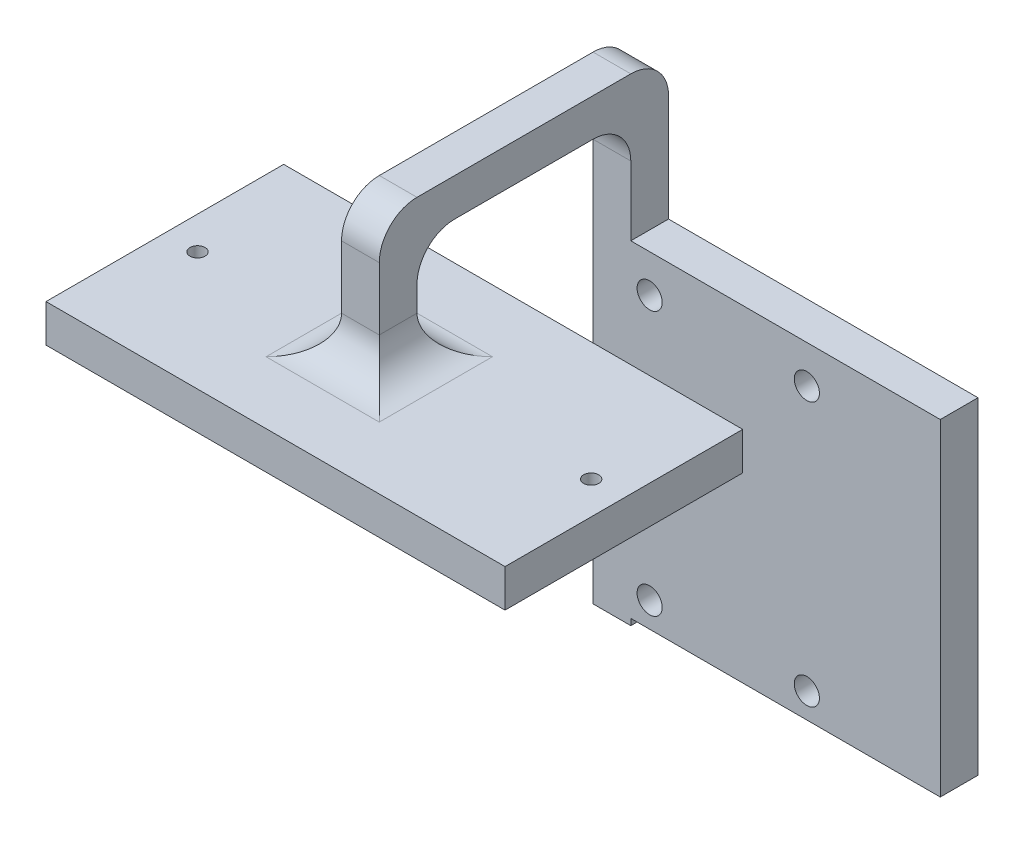
SolidWorks part; units mm, degrees
ref_plane "Ön Düzlem" through (0, 0, 0) normal (0, 0, 1) x (1, 0, 0)
ref_plane "Üst Düzlem" through (0, 0, 0) normal (0, 1, 0) x (1, 0, 0)
ref_plane "Sağ Düzlem" through (0, 0, 0) normal (1, 0, 0) x (0, 0, -1)
sketch "Çizim1" plane through (0, 0, 0) normal (0, 1, 0) x (1, 0, 0)
  line L13 (-14.05, 0) -> (-19.1293, 0) construction
  line L14 (0, 6.45) -> (0, 11.0365) construction
  line L22 (21.5293, 0) -> (16.45, 0) construction
  line L23 (0, -11.0365) -> (0, -6.45) construction
  line L24 (-19.1293, 11.0365) -> (21.5293, 11.0365)
  line L25 (-19.1293, 11.0365) -> (-19.1293, -11.0365)
  line L26 (-19.1293, -11.0365) -> (21.5293, -11.0365)
  line L27 (1.9, -6.45) -> (1.9, -3.2953)
  line L28 (1.9, -3.2953) -> (16.6263, -1.9922)
  line L29 (16.6263, 1.9922) -> (1.9, 3.2953)
  line L30 (1.9, 3.2953) -> (1.9, 6.45)
  line L31 (-1.9, 6.45) -> (-1.9, 2.8797)
  line L32 (-2.2091, 2.65) -> (-14.1591, 1.997)
  line L33 (-14.1591, -1.997) -> (-2.2091, -2.65)
  line L34 (-1.9, -2.8797) -> (-1.9, -6.45)
  line L35 (21.5293, 11.0365) -> (21.5293, -11.0365)
  arc A19 (-1.9, -6.45) -> (1.9, -6.45) centre (0, -6.45) ccw
  arc A20 (16.6263, -1.9922) -> (16.6263, 1.9922) centre (16.45, 0) ccw
  arc A21 (1.9, 6.45) -> (-1.9, 6.45) centre (0, 6.45) ccw
  arc A22 (-1.9, 2.8797) -> (-2.2091, 2.65) centre (0, 0) ccw
  arc A23 (-14.1591, 1.997) -> (-14.1591, -1.997) centre (-14.05, 0) ccw
  arc A24 (-2.2091, -2.65) -> (-1.9, -2.8797) centre (0, 0) ccw
extrude "Yükseklik-Ekstrüzyon3" add sketch "Çizim1" along normal blind 1.5
sketch "Çizim10" plane through (0, 1.5, 0) normal (0, 1, 0) x (1, 0, 0)
  line L4 (21.5293, -11.0365) -> (21.5293, 11.0365)
  line L5 (21.5293, 11.0365) -> (-19.1293, 11.0365)
  line L6 (-19.1293, 11.0365) -> (-19.1293, -11.0365)
  line L7 (-19.1293, -11.0365) -> (21.5293, -11.0365)
  line L8 (21.5293, -11.0365) -> (21.5293, 11.0365)
  line L9 (21.5293, 11.0365) -> (-19.1293, 11.0365)
  line L10 (-19.1293, 11.0365) -> (-19.1293, -11.0365)
  line L11 (-19.1293, -11.0365) -> (21.5293, -11.0365)
  dimension "D1" = 0
extrude "Yükseklik-Ekstrüzyon5" add sketch "Çizim10" along normal blind 1.5
sketch "Çizim11" plane through (0, 0, 0) normal (1, 0, 0) x (0, 0, -1)
  line L2 (18.5, 10.9809) -> (1.5, 10.9809)
  line L3 (18.5, 10.9809) -> (18.5, -24.0191)
  line L4 (1.5, 1.7777) -> (1.5, 10.9809)
  line L5 (1.5, 13.9809) -> (21.5, 13.9809)
  line L6 (21.5, 13.9809) -> (21.5, -24.0191)
  line L7 (-1.5, 1.7777) -> (-1.5, 10.9809)
  line L8 (18.5, -24.0191) -> (21.5, -24.0191)
  line L9 (1.5, 1.7777) -> (-1.5, 1.7777)
  line L10 (0, 1.7777) -> (0, 10.9809) construction
  line L11 (18.5, 10.9809) -> (18.5, 13.9809) construction
  line L12 (18.5, 12.4809) -> (-13.0492, 12.4809) construction
  line L13 (18.5, 12.4809) -> (21.5, 12.4809) construction
  line L14 (20, 12.4809) -> (20, -24.0191) construction
  line L15 (1.5, 13.9809) -> (-1.5, 13.9809)
  line L16 (-1.5, 13.9809) -> (-1.5, 10.9809)
  line L18 (0, 12.4809) -> (0, 15.9654) construction
  dimension "D1" = 20
  dimension "D2" = 3
  dimension "D3" = 3
  dimension "D4" = 3
  dimension "D5" = 36.5
extrude "Yükseklik-Ekstrüzyon6" add sketch "Çizim11" along normal mid plane 3
sketch "Çizim12" plane through (0, 0, 0) normal (0, 1, 0) x (1, 0, 0)
  line L0 (-14.05, 0) -> (-17.05, 0) construction
  line L1 (19.45, 0) -> (16.45, 0) construction
  line L2 (0, -6.45) -> (0, -9.45) construction
  line L3 (0, 9.45) -> (0, 6.45) construction
  line L4 (0, -9.45) -> (-17.05, -9.45)
  line L5 (-17.05, -9.45) -> (-17.05, 9.45)
  line L6 (-17.05, 9.45) -> (19.45, 9.45)
  line L7 (19.45, 9.45) -> (19.45, -9.45)
  line L8 (19.45, -9.45) -> (0, -9.45)
  line L10 (-19.1293, -11.0365) -> (21.5293, -11.0365)
  line L11 (-19.1293, -11.0365) -> (-19.1293, 11.0365)
  line L12 (-19.1293, 11.0365) -> (21.5293, 11.0365)
  line L13 (21.5293, -11.0365) -> (21.5293, 11.0365)
  dimension "D1" = 3
  dimension "D2" = 3
extrude "Kes-Ekstrüzyon1" cut sketch "Çizim12" along normal blind 5 and the other way blind 3
fillet "Radyus1" radius 3 8 edges at (0, 3, -1.5) (-1.5, 3, 0) (1.5, 3, 0) (0, 3, 1.5) (0, 13.9809, 1.5) (0, 10.9809, -1.5) (0, 13.9809, -21.5) (0, 10.9809, -18.5)
ref_plane "Düzlem1" through (0, 0, -20) normal (0, 0, -1) x (-1, 0, 0)
sketch "Çizim13" plane through (0, 0, -20) normal (0, 0, -1) x (-1, 0, 0)
  line L0 (-26.1083, 2.483) -> (-26.1083, -23.517)
  line L3 (0.8917, 2.483) -> (0.8917, -2.4979)
  line L8 (0.8917, 2.483) -> (-26.1083, 2.483)
  line L16 (0.8917, -23.517) -> (-26.1083, -23.517)
  line L22 (0.8917, -2.4979) -> (0.8917, -23.517)
  point P0 (-12.6083, -23.517)
  dimension "D2" = 27
  dimension "D1" = 26
extrude "Yükseklik-Ekstrüzyon7" add sketch "Çizim13" along normal up to surface and the other way up to surface up to face at (0, -6.5191, -21.5) other way up to face at (0, -8.0191, -18.5)
sketch "Çizim18" plane through (0, 1.5, 0) normal (0, -1, 0) x (1, 0, 0)
  line L0 (-16.05, 0) -> (-14.45, 0) construction
  line L1 (18.45, 0) -> (16.85, 0) construction
  arc A0 (-14.1591, 1.997) -> (-14.1591, -1.997) centre (-14.05, 0) ccw construction
  circle A1 centre (-14.45, 0) radius 0.6
  arc A2 (16.6263, -1.9922) -> (16.6263, 1.9922) centre (16.45, 0) ccw construction
  circle A3 centre (16.85, 0) radius 0.6
extrude "Kes-Ekstrüzyon3" cut sketch "Çizim18" against normal blind 3 and the other way blind 7
sketch "Sketch1" plane through (0, 0, -21.5) normal (0, 0, -1) x (-1, 0, 0)
  line L0 (-1.5, -23.517) -> (-26.1083, -23.517) construction
  line L1 (1.5, -24.0191) -> (1.5, 10.9809) construction
  line L2 (-26.1083, 2.483) -> (-1.5, 2.483) construction
  circle A0 centre (-2.999, -0.517) radius 1
  circle A1 centre (-2.999, -21.517) radius 1
  circle A2 centre (-15.499, -21.517) radius 1
  circle A3 centre (-15.499, -0.517) radius 1
  point P10 (0, 0)
  point P13 (0, 0)
  dimension "D1" = 2
  dimension "D2" = 2
  dimension "D3" = 2
  dimension "D4" = 2
  dimension "D7" = 2
  dimension "D5" = 21
  dimension "D6" = 21
  dimension "D8" = 3
  dimension "D9" = 3
  dimension "D10" = 2
  dimension "D11" = 12.5
  dimension "D12" = 12.5
  dimension "D13" = 4.499
extrude "Cut-Extrude1" cut sketch "Sketch1" against normal up to surface (3 mm away) up to face at (6.9021, -9.268, -18.5)
